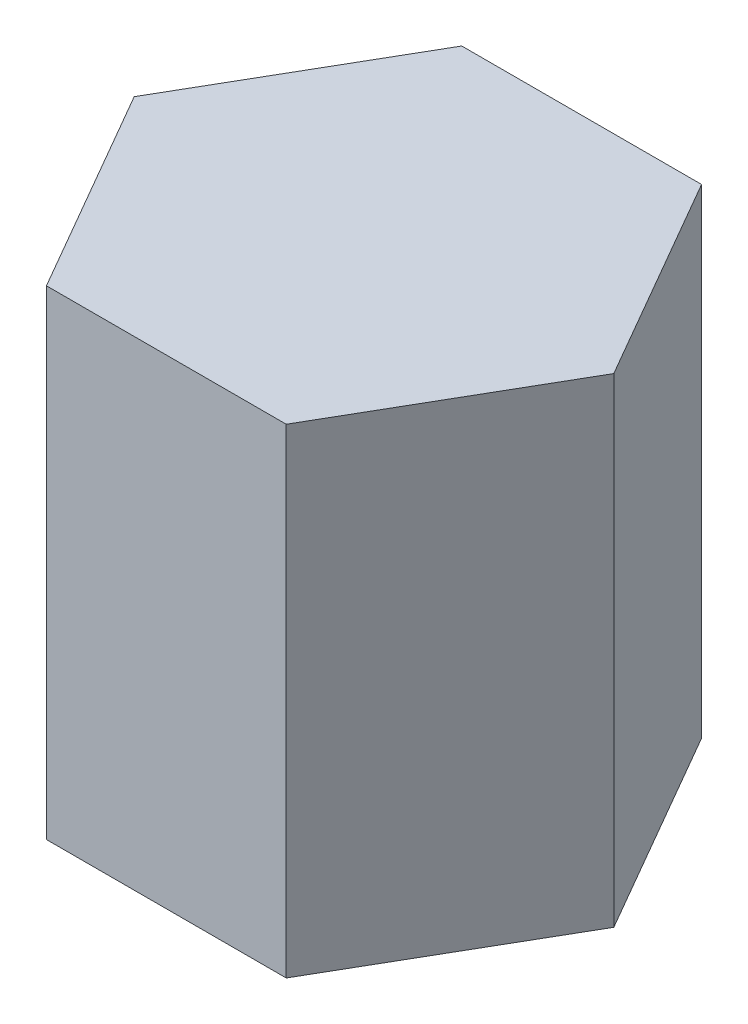
SolidWorks part; units mm, degrees
ref_plane "Front Plane" through (0, 0, 0) normal (0, 0, 1) x (1, 0, 0)
ref_plane "Top Plane" through (0, 0, 0) normal (0, 1, 0) x (1, 0, 0)
ref_plane "Right Plane" through (0, 0, 0) normal (1, 0, 0) x (0, 0, -1)
sketch "Sketch1" plane through (0, 0, 0) normal (0, 1, 0) x (1, 0, 0)
  line L0 (0, 0) -> (-25.4, 0)
  line L2 (-25.4, 43.9941) -> (-38.1, 21.997)
  line L3 (0, 43.9941) -> (-25.4, 43.9941)
  line L4 (-38.1, 21.997) -> (-25.4, 0)
  line L5 (0, 0) -> (12.7, 21.997)
  line L6 (0, 43.9941) -> (12.7, 21.997)
extrude "Boss-Extrude1" add sketch "Sketch1" along normal blind 50.8 contours L2 L4 L0 L5 L6 L3
